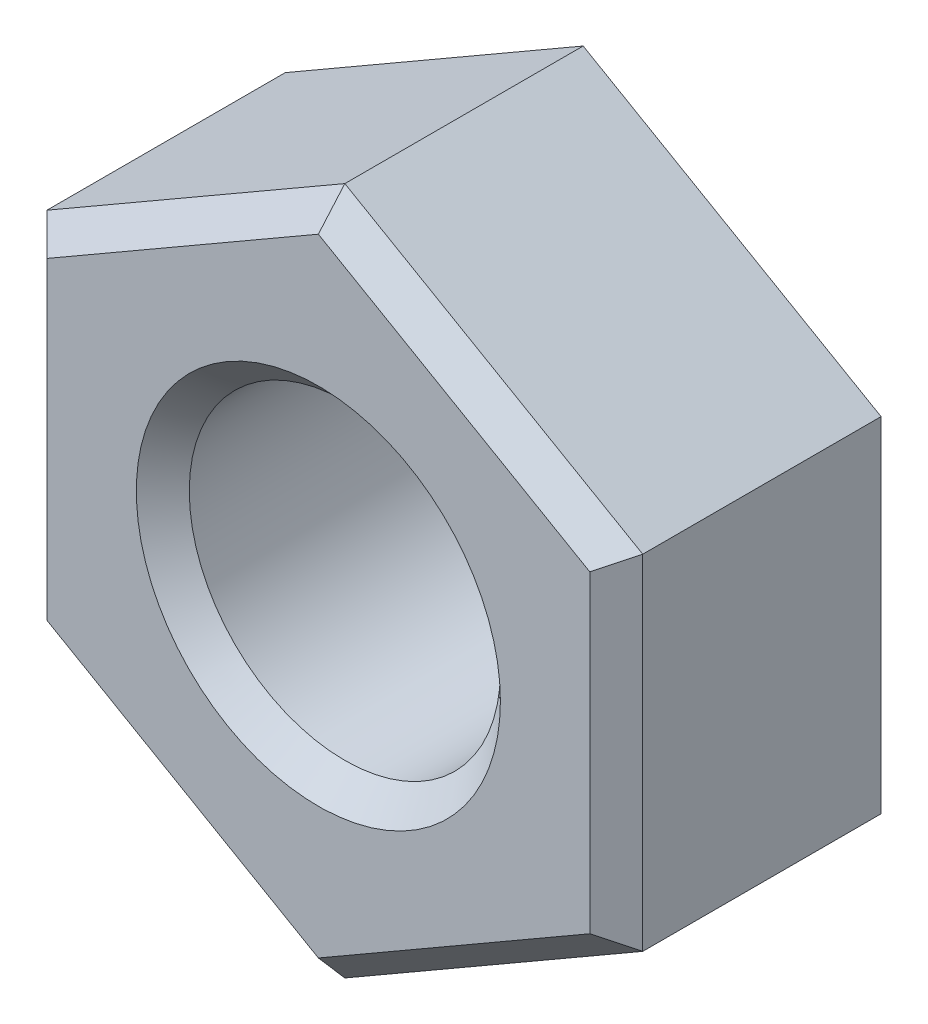
SolidWorks part; units mm, degrees
ref_plane "Front Plane" through (0, 0, 0) normal (0, 0, 1) x (1, 0, 0)
ref_plane "Top Plane" through (0, 0, 0) normal (0, 1, 0) x (1, 0, 0)
ref_plane "Right Plane" through (0, 0, 0) normal (1, 0, 0) x (0, 0, -1)
sketch "Sketch1" plane through (0, 0, 0) normal (0, 0, 1) x (1, 0, 0)
  line L1 (4.5, -2.5981) -> (4.5, 2.5981)
  line L2 (4.5, 2.5981) -> (0, 5.1962)
  line L3 (0, 5.1962) -> (-4.5, 2.5981)
  line L4 (-4.5, 2.5981) -> (-4.5, -2.5981)
  line L5 (-4.5, -2.5981) -> (0, -5.1962)
  line L6 (0, -5.1962) -> (4.5, -2.5981)
  circle A0 centre (0, 0) radius 4.5 construction
  circle A1 centre (0, 0) radius 2.35
  point P9 (-0.3301, -9.3335)
  point P10 (0, 0)
  point P11 (0, 0)
  dimension "D2" = 4.7
  dimension "D1" = 9
extrude "Boss-Extrude1" add sketch "Sketch1" along normal blind 4
chamfer "Chamfer1" distance 0.4 angle 45 7 edges at (2.35, 0, 4) (-2.25, -3.8971, 4) (-4.5, 0, 4) (-2.25, 3.8971, 4) (2.25, 3.8971, 4) (4.5, 0, 4) (2.25, -3.8971, 4)
